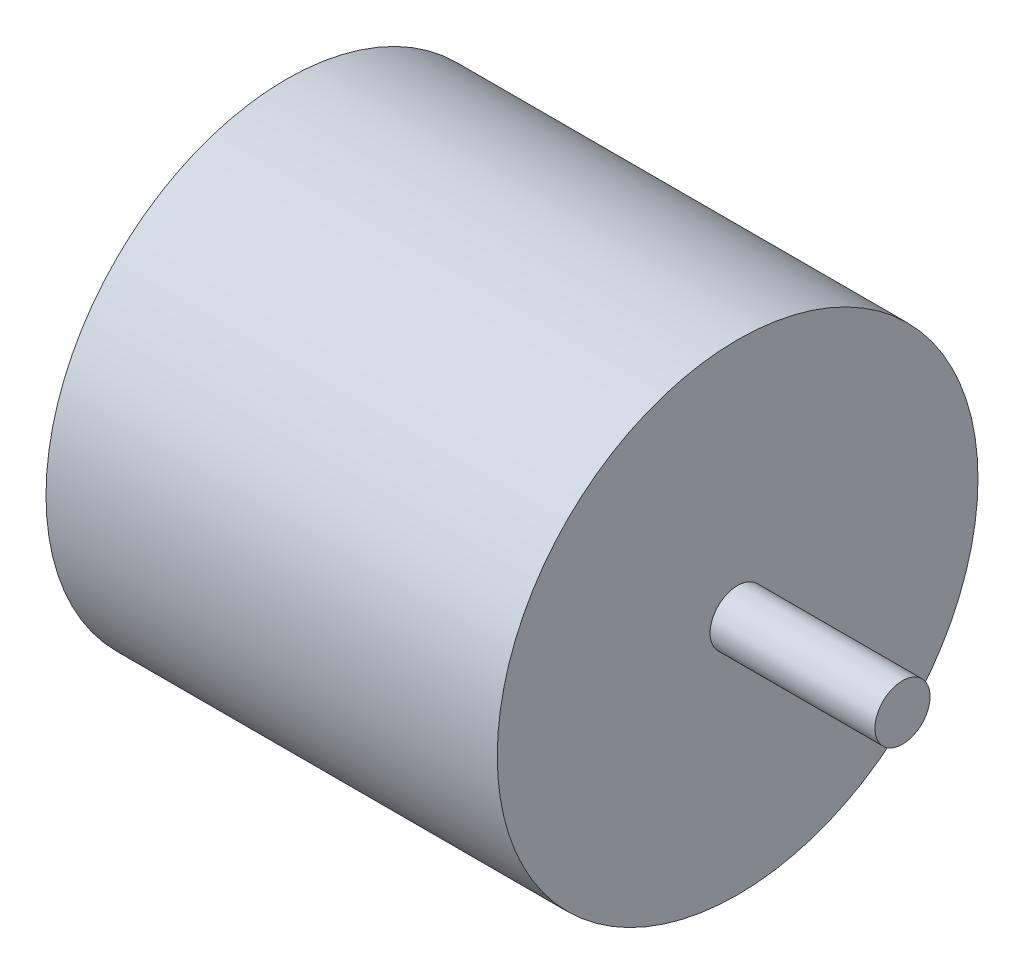
SolidWorks part; units mm, degrees
ref_plane "Front Plane" through (0, 0, 0) normal (0, 0, 1) x (1, 0, 0)
ref_plane "Top Plane" through (0, 0, 0) normal (0, 1, 0) x (1, 0, 0)
ref_plane "Right Plane" through (0, 0, 0) normal (1, 0, 0) x (0, 0, -1)
sketch "Sketch1" plane through (0, 0, 0) normal (0, 0, 1) x (1, 0, 0)
  line L0 (-313.7592, 0) -> (15374.2029, 0) construction
  line L1 (-14.5, 0) -> (-14.5, 1.5875)
  line L2 (-14.5, 1.5875) -> (-13, 1.5875)
  line L3 (-13, 1.5875) -> (-13, 13.85)
  line L4 (-13, 13.85) -> (13, 13.85)
  line L5 (13, 13.85) -> (13, 1.5875)
  line L6 (13, 1.5875) -> (22.5, 1.5875)
  line L7 (22.5, 1.5875) -> (22.5, 0)
  line L8 (-14.5, 0) -> (22.5, 0)
  point P5 (0, 13.85)
  dimension "D1" = 27.7
  dimension "D2" = 26
  dimension "D3" = 9.5
  dimension "D4" = 37
  dimension "D5" = 3.175
revolve "Revolve1" add sketch "Sketch1" angle 360 about L0
